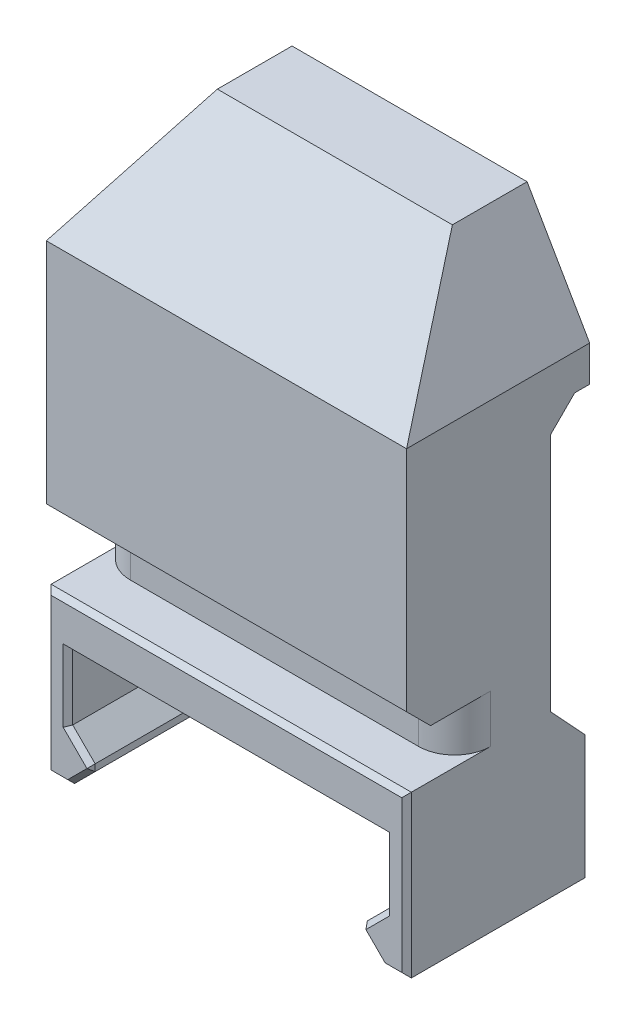
SolidWorks part; units mm, degrees
material "PLA"
ref_plane "Front Plane" through (0, 0, 0) normal (0, 0, 1) x (1, 0, 0)
ref_plane "Top Plane" through (0, 0, 0) normal (0, 1, 0) x (1, 0, 0)
ref_plane "Right Plane" through (0, 0, 0) normal (1, 0, 0) x (0, 0, -1)
sketch "Sketch1" plane through (0, 0, 0) normal (1, 0, 0) x (0, 0, -1)
  line L5 (-7.625, 6.7) -> (-3.625, 6.7)
  line L7 (-7.625, 6.7) -> (-7.625, -6.7)
  line L8 (-7.625, -6.7) -> (7.625, -6.7)
  line L9 (7.625, 3.2) -> (7.625, -6.7)
  line L11 (-3.625, 6.7) -> (-3.625, 10.7)
  line L12 (-3.625, 10.7) -> (-7.625, 10.7)
  line L13 (4.375, 6.7) -> (7.625, 3.2)
  line L14 (4.375, 6.7) -> (4.375, 26.7)
  line L15 (-7.625, 10.7) -> (-7.625, 31.6706)
  line L16 (4.375, 26.7) -> (6.375, 28.7)
  line L18 (1.4044, 40.7) -> (-7.625, 31.6706)
  line L19 (6.375, 28.7) -> (7.625, 28.7)
  line L20 (7.625, 28.7) -> (7.625, 40.7)
  line L21 (7.625, 40.7) -> (1.4044, 40.7)
  point P3 (-7.625, 0)
  point P6 (0, -6.7)
  dimension "D1" = 13.4
  dimension "D2" = 15.25
  dimension "D3" = 3.25
  dimension "D4" = 3.5
  dimension "D5" = 4
  dimension "D6" = 4
  dimension "D7" = 20
  dimension "D8" = 45
  dimension "D9" = 2
  dimension "D10" = 1.25
  dimension "D11" = 12
  dimension "D12" = 12
  dimension "D13" = 4
extrude "Boss-Extrude1" add sketch "Sketch1" along normal mid plane 30
fillet "Fillet1" radius 3 2 edges at (-15, 8.7, 3.625) (15, 8.7, 3.625)
sketch "Sketch2" plane through (0, 0, 7.625) normal (0, 0, 1) x (1, 0, 0)
  line L0 (15, -6.7) -> (-15, -6.7) construction
  line L1 (-13.2, 2.9) -> (13.2, 2.9)
  line L2 (-13.2, 2.9) -> (-13.2, -2.55)
  line L3 (-13.05, -6.7) -> (13.05, -6.7)
  line L4 (13.2, 2.9) -> (13.2, -2.55)
  line L5 (-13.05, -6.7) -> (-11.05, -4.7)
  line L6 (-11.05, -4.7) -> (-13.2, -2.55)
  line L7 (13.05, -6.7) -> (11.05, -4.7)
  line L8 (11.05, -4.7) -> (13.2, -2.55)
  line L9 (-15, 6.7) -> (-15, -6.7) construction
  line L10 (15, 6.7) -> (15, -6.7) construction
  dimension "D1" = 9.6
  dimension "D2" = 1.95
  dimension "D3" = 1.95
  dimension "D4" = 2
  dimension "D5" = 2
  dimension "D6" = 2
  dimension "D7" = 2
  dimension "D8" = 1.8
  dimension "D9" = 1.8
extrude "Cut-Extrude1" cut sketch "Sketch2" against normal through all
chamfer "Chamfer1" distance 0.4 angle 45 24 edges at (13.2, 0.175, 7.625) (0, 2.9, 7.625) (-13.2, 0.175, 7.625) (-12.125, -3.625, 7.625) (-12.05, -5.7, 7.625) (-14.025, -6.7, 7.625) (-15, 0, 7.625) (0, 6.7, 7.625) (15, 0, 7.625) (14.025, -6.7, 7.625) (12.05, -5.7, 7.625) (12.125, -3.625, 7.625) (11.05, -4.7, 0) (-11.05, -4.7, 0) (15, -1.75, -7.625) (14.025, -6.7, -7.625) (13.2, 0.175, -7.625) (12.125, -3.625, -7.625) (12.05, -5.7, -7.625) (-15, -1.75, -7.625) (-13.2, 0.175, -7.625) (-12.125, -3.625, -7.625) (-14.025, -6.7, -7.625) (-12.05, -5.7, -7.625)
sketch "Sketch3" plane through (0, 0, 7.625) normal (0, 0, 1) x (1, 0, 0)
  line L0 (-15, 31.6706) -> (-9.7869, 40.7)
  line L1 (15, 40.7) -> (-15, 40.7) construction
  line L2 (-9.7869, 40.7) -> (-15, 40.7)
  line L3 (-15, 40.7) -> (-15, 31.6706)
  line L4 (15, 31.6706) -> (15, 40.7)
  line L5 (15, 40.7) -> (9.7869, 40.7)
  line L6 (9.7869, 40.7) -> (15, 31.6706)
  dimension "D1" = 30
  dimension "D2" = 30
extrude "Cut-Extrude2" cut sketch "Sketch3" against normal through all
chamfer "Chamfer2" distance 2 angle 45 1 edges at (0, 10.7, 7.625)
